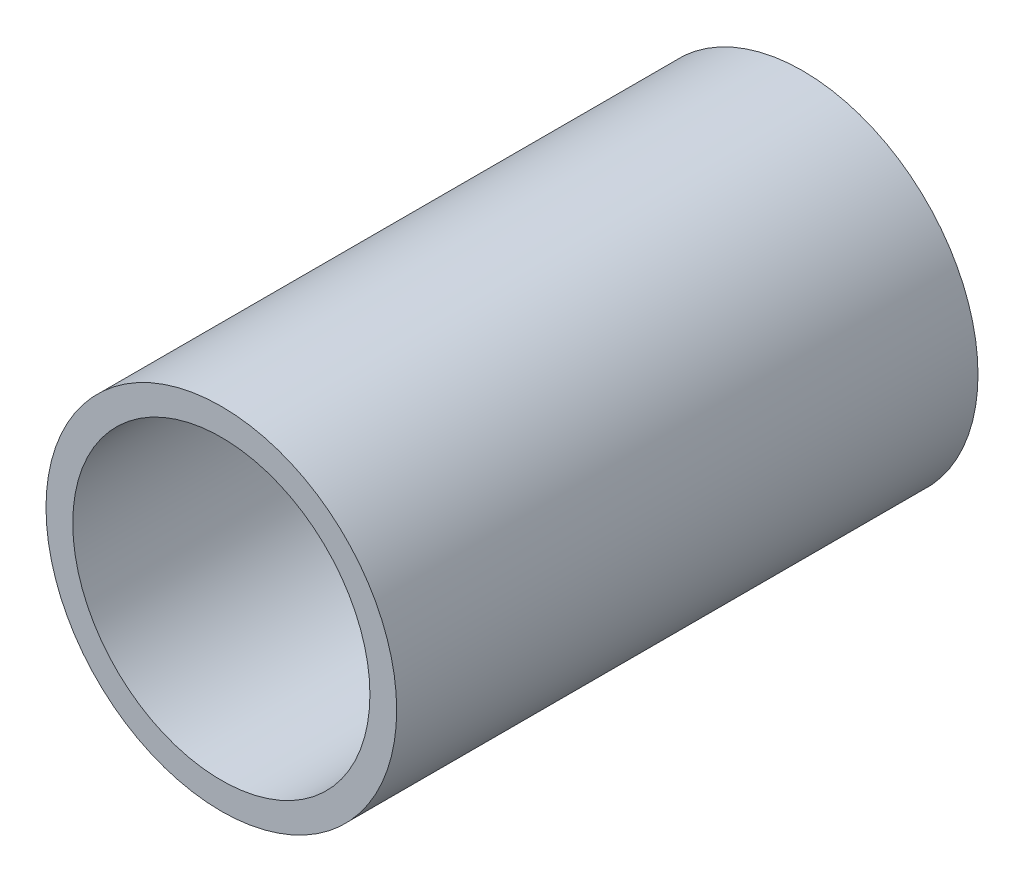
SolidWorks part; units mm, degrees
ref_plane "Front Plane" through (0, 0, 0) normal (0, 0, 1) x (1, 0, 0)
ref_plane "Top Plane" through (0, 0, 0) normal (0, 1, 0) x (1, 0, 0)
ref_plane "Right Plane" through (0, 0, 0) normal (1, 0, 0) x (0, 0, -1)
sketch "Sketch1" plane through (0, 0, 0) normal (0, 0, 1) x (1, 0, 0)
  circle A0 centre (0, 0) radius 24.13
  dimension "Pipe OD" = 48.26
extrude "Extrude-Thin1" add sketch "Sketch1" along normal mid plane 80 thin thin type one direction reverse wall 3.683
